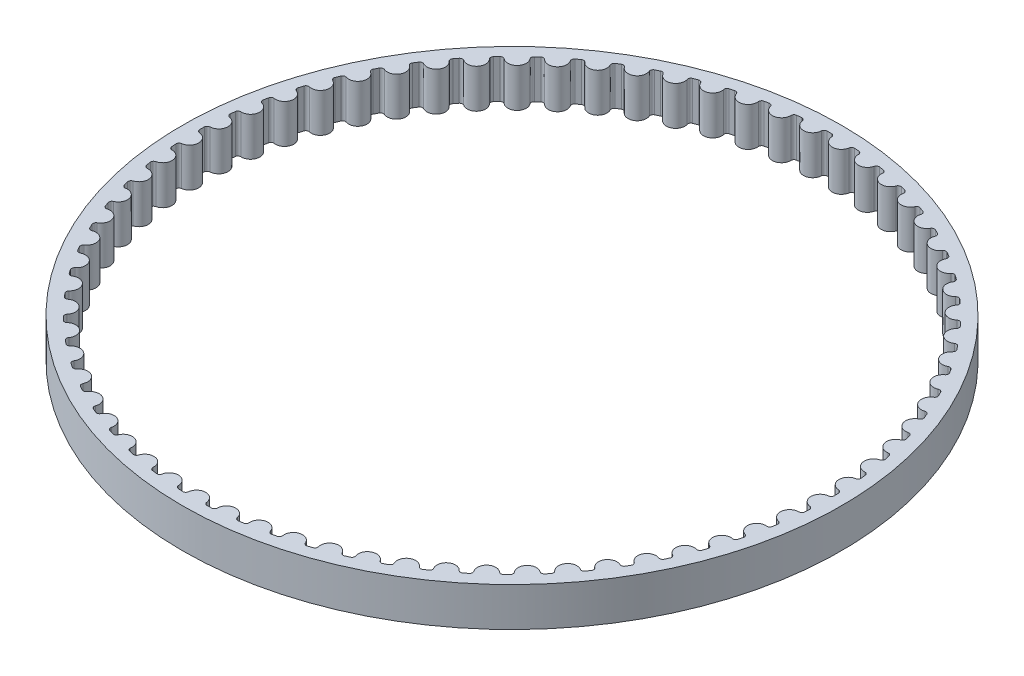
SolidWorks part; units mm, degrees
ref_plane "Front Plane" through (0, 0, 0) normal (0, 0, 1) x (1, 0, 0)
ref_plane "Top Plane" through (0, 0, 0) normal (0, 1, 0) x (1, 0, 0)
ref_plane "Right Plane" through (0, 0, 0) normal (1, 0, 0) x (0, 0, -1)
sketch "Sketch1" plane through (0, 0, 0) normal (0, 1, 0) x (1, 0, 0)
  circle A0 centre (0, 0) radius 33.8241
  arc B0 (-1.7169, -32.5188) -> (-1.2473, -32.5402) centre (0, 0) ccw
  arc B1 (-1.2473, -32.5402) -> (-0.9385, -32.2732) centre (-1.2358, -32.2414) ccw
  arc B2 (0.9385, -32.2732) -> (-0.9385, -32.2732) centre (0, -32.3736) ccw
  arc B3 (0.9385, -32.2732) -> (1.2473, -32.5402) centre (1.2358, -32.2414) ccw
  arc B4 (1.2473, -32.5402) -> (1.7169, -32.5188) centre (0, 0) ccw
  arc B5 (1.7169, -32.5188) -> (2.0001, -32.2248) centre (1.7011, -32.2202) ccw
  arc B6 (3.8694, -32.0541) -> (2.0001, -32.2248) centre (2.9439, -32.2394) ccw
  arc B7 (3.8694, -32.0541) -> (4.2012, -32.2919) centre (4.1626, -31.9954) ccw
  arc B8 (4.2012, -32.2919) -> (4.6669, -32.2279) centre (0, 0) ccw
  arc B9 (4.6669, -32.2279) -> (4.9222, -31.9094) centre (4.624, -31.932) ccw
  arc B10 (6.7682, -31.5695) -> (4.9222, -31.9094) centre (5.8634, -31.8382) ccw
  arc B11 (6.7682, -31.5695) -> (7.1202, -31.7761) centre (7.0548, -31.4843) ccw
  arc B12 (7.1202, -31.7761) -> (7.5782, -31.67) centre (0, 0) ccw
  arc B13 (7.5782, -31.67) -> (7.8035, -31.3296) centre (7.5086, -31.3792) ccw
  arc B14 (9.6109, -30.8232) -> (7.8035, -31.3296) centre (8.7343, -31.1731) ccw
  arc B15 (9.6109, -30.8232) -> (9.9803, -30.997) centre (9.8886, -30.7124) ccw
  arc B16 (9.9803, -30.997) -> (10.4267, -30.8497) centre (0, 0) ccw
  arc B17 (10.4267, -30.8497) -> (10.6201, -30.4902) centre (10.331, -30.5664) ccw
  arc B18 (12.374, -29.8215) -> (10.6201, -30.4902) centre (11.5328, -30.2497) ccw
  arc B19 (12.374, -29.8215) -> (12.7576, -29.961) centre (12.6405, -29.6859) ccw
  arc B20 (12.7576, -29.961) -> (13.1888, -29.7737) centre (0, 0) ccw
  arc B21 (13.1888, -29.7737) -> (13.3487, -29.3982) centre (13.0677, -29.5003) ccw
  arc B22 (15.0346, -28.5727) -> (13.3487, -29.3982) centre (14.2358, -29.0756) ccw
  arc B23 (15.0346, -28.5727) -> (15.4293, -28.6768) centre (15.2876, -28.4135) ccw
  arc B24 (15.4293, -28.6768) -> (15.8416, -28.451) centre (0, 0) ccw
  arc B25 (15.8416, -28.451) -> (15.9667, -28.0625) centre (15.6962, -28.1898) ccw
  arc B26 (17.5705, -27.0872) -> (15.9667, -28.0625) centre (16.8208, -27.6606) ccw
  arc B27 (17.5705, -27.0872) -> (17.9731, -27.1549) centre (17.808, -26.9056) ccw
  arc B28 (17.9731, -27.1549) -> (18.3632, -26.8926) centre (0, 0) ccw
  arc B29 (18.3632, -26.8926) -> (18.4524, -26.4943) centre (18.1946, -26.6457) ccw
  arc B30 (19.9609, -25.3772) -> (18.4524, -26.4943) centre (19.2664, -26.0164) ccw
  arc B31 (19.9609, -25.3772) -> (20.3679, -25.408) centre (20.1809, -25.1747) ccw
  arc B32 (20.3679, -25.408) -> (20.7326, -25.1113) centre (0, 0) ccw
  arc B33 (20.7326, -25.1113) -> (20.7852, -24.7066) centre (20.5422, -24.8808) ccw
  arc B34 (22.1859, -23.4569) -> (20.7852, -24.7066) centre (21.5524, -24.1566) ccw
  arc B35 (22.1859, -23.4569) -> (22.594, -23.4506) centre (22.3866, -23.2353) ccw
  arc B36 (22.594, -23.4506) -> (22.9302, -23.122) centre (0, 0) ccw
  arc B37 (22.9302, -23.122) -> (22.9458, -22.7141) centre (22.7196, -22.9097) ccw
  arc B38 (24.227, -21.3423) -> (22.9458, -22.7141) centre (23.6598, -22.0967) ccw
  arc B39 (24.227, -21.3423) -> (24.6329, -21.2988) centre (24.4067, -21.1033) ccw
  arc B40 (24.6329, -21.2988) -> (24.9378, -20.941) centre (0, 0) ccw
  arc B41 (24.9378, -20.941) -> (24.9162, -20.5334) centre (24.7088, -20.7487) ccw
  arc B42 (26.0674, -19.0508) -> (24.9162, -20.5334) centre (25.5711, -19.8536) ccw
  arc B43 (26.0674, -19.0508) -> (26.4676, -18.9706) centre (26.2246, -18.7964) ccw
  arc B44 (26.4676, -18.9706) -> (26.7387, -18.5865) centre (0, 0) ccw
  arc B45 (26.7387, -18.5865) -> (26.6802, -18.1826) centre (26.4932, -18.4159) ccw
  arc B46 (27.6918, -16.6014) -> (26.6802, -18.1826) centre (27.2705, -17.4461) ccw
  arc B47 (27.6918, -16.6014) -> (28.0831, -16.4852) centre (27.8252, -16.3338) ccw
  arc B48 (28.0831, -16.4852) -> (28.3181, -16.078) centre (0, 0) ccw
  arc B49 (28.3181, -16.078) -> (28.2231, -15.6811) centre (28.0581, -15.9304) ccw
  arc B50 (29.0867, -14.0145) -> (28.2231, -15.6811) centre (28.744, -14.8939) ccw
  arc B51 (29.0867, -14.0145) -> (29.4658, -13.8631) centre (29.1952, -13.7359) ccw
  arc B52 (29.4658, -13.8631) -> (29.6628, -13.4363) centre (0, 0) ccw
  arc B53 (29.6628, -13.4363) -> (29.5321, -13.0496) centre (29.3905, -13.313) ccw
  arc B54 (30.2406, -11.3114) -> (29.5321, -13.0496) centre (29.9793, -12.2184) ccw
  arc B55 (30.2406, -11.3114) -> (30.6043, -11.1262) centre (30.3233, -11.0241) ccw
  arc B56 (30.6043, -11.1262) -> (30.7618, -10.6833) centre (0, 0) ccw
  arc B57 (30.7618, -10.6833) -> (30.5964, -10.3101) centre (30.4793, -10.5852) ccw
  arc B58 (31.1439, -8.5146) -> (30.5964, -10.3101) centre (30.9662, -9.4416) ccw
  arc B59 (31.1439, -8.5146) -> (31.4893, -8.2971) centre (31.2002, -8.221) ccw
  arc B60 (31.4893, -8.2971) -> (31.6058, -7.8417) centre (0, 0) ccw
  arc B61 (31.6058, -7.8417) -> (31.4072, -7.4851) centre (31.3156, -7.7697) ccw
  arc B62 (31.7891, -5.6473) -> (31.4072, -7.4851) centre (31.6965, -6.5866) ccw
  arc B63 (31.7891, -5.6473) -> (32.1133, -5.3993) centre (31.8185, -5.3497) ccw
  arc B64 (32.1133, -5.3993) -> (32.1879, -4.9351) centre (0, 0) ccw
  arc B65 (32.1879, -4.9351) -> (31.9578, -4.5981) centre (31.8924, -4.8898) ccw
  arc B66 (32.1709, -2.7331) -> (31.9578, -4.5981) centre (32.1641, -3.677) ccw
  arc B67 (32.1709, -2.7331) -> (32.4713, -2.4567) centre (32.1731, -2.4341) ccw
  arc B68 (32.4713, -2.4567) -> (32.5034, -1.9877) centre (0, 0) ccw
  arc B69 (32.5034, -1.9877) -> (32.2435, -1.6729) centre (32.2049, -1.9694) ccw
  arc B70 (32.2862, 0.2036) -> (32.2435, -1.6729) centre (32.3652, -0.7369) ccw
  arc B71 (32.2862, 0.2036) -> (32.5601, 0.5062) centre (32.2612, 0.5016) ccw
  arc B72 (32.5601, 0.5062) -> (32.5494, 0.9762) centre (0, 0) ccw
  arc B73 (32.5494, 0.9762) -> (32.262, 1.2661) centre (32.2506, 0.9673) ccw
  arc B74 (32.1339, 3.1387) -> (32.262, 1.2661) centre (32.2981, 2.2093) ccw
  arc B75 (32.1339, 3.1387) -> (32.3792, 3.465) centre (32.0819, 3.4332) ccw
  arc B76 (32.3792, 3.465) -> (32.3258, 3.9321) centre (0, 0) ccw
  arc B77 (32.3258, 3.9321) -> (32.0132, 4.1946) centre (32.029, 3.896) ccw
  arc B78 (31.7154, 6.0478) -> (32.0132, 4.1946) centre (31.9634, 5.1371) ccw
  arc B79 (31.7154, 6.0478) -> (31.93, 6.395) centre (31.6368, 6.3363) ccw
  arc B80 (31.93, 6.395) -> (31.8343, 6.8553) centre (0, 0) ccw
  arc B81 (31.8343, 6.8553) -> (31.4991, 7.0883) centre (31.542, 6.7924) ccw
  arc B82 (31.034, 8.9068) -> (31.4991, 7.0883) centre (31.3638, 8.0224) ccw
  arc B83 (31.034, 8.9068) -> (31.2161, 9.2721) centre (30.9295, 9.187) ccw
  arc B84 (31.2161, 9.2721) -> (31.079, 9.7218) centre (0, 0) ccw
  arc B85 (31.079, 9.7218) -> (30.7241, 9.9233) centre (30.7937, 9.6325) ccw
  arc B86 (30.0955, 11.692) -> (30.7241, 9.9233) centre (30.5044, 10.8412) ccw
  arc B87 (30.0955, 11.692) -> (30.2436, 12.0723) centre (29.966, 11.9615) ccw
  arc B88 (30.2436, 12.0723) -> (30.0662, 12.5077) centre (0, 0) ccw
  arc B89 (30.0662, 12.5077) -> (29.6944, 12.6761) centre (29.7902, 12.3928) ccw
  arc B90 (28.9076, 14.3803) -> (29.6944, 12.6761) centre (29.3921, 13.5702) ccw
  arc B91 (28.9076, 14.3803) -> (29.0205, 14.7725) centre (28.7541, 14.6369) ccw
  arc B92 (29.0205, 14.7725) -> (28.8043, 15.1899) centre (0, 0) ccw
  arc B93 (28.8043, 15.1899) -> (28.4187, 15.3238) centre (28.5398, 15.0504) ccw
  arc B94 (27.4801, 16.9494) -> (28.4187, 15.3238) centre (28.0363, 16.1868) ccw
  arc B95 (27.4801, 16.9494) -> (27.557, 17.3503) centre (27.3039, 17.191) ccw
  arc B96 (27.557, 17.3503) -> (27.3036, 17.7463) centre (0, 0) ccw
  arc B97 (27.3036, 17.7463) -> (26.9075, 17.8446) centre (27.0529, 17.5833) ccw
  arc B98 (25.825, 19.3781) -> (26.9075, 17.8446) centre (26.4482, 18.6692) ccw
  arc B99 (25.825, 19.3781) -> (25.8651, 19.7843) centre (25.6276, 19.6026) ccw
  arc B100 (25.8651, 19.7843) -> (25.5768, 20.1556) centre (0, 0) ccw
  arc B101 (25.5768, 20.1556) -> (25.1733, 20.2175) centre (25.3419, 19.9705) ccw
  arc B102 (23.9559, 21.6462) -> (25.1733, 20.2175) centre (24.641, 20.9969) ccw
  arc B103 (23.9559, 21.6462) -> (23.9588, 22.0543) centre (23.7388, 21.8518) ccw
  arc B104 (23.9588, 22.0543) -> (23.6379, 22.3979) centre (0, 0) ccw
  arc B105 (23.6379, 22.3979) -> (23.2305, 22.4228) centre (23.4209, 22.1923) ccw
  arc B106 (21.8882, 23.7349) -> (23.2305, 22.4228) centre (22.6295, 23.1506) ccw
  arc B107 (21.8882, 23.7349) -> (21.854, 24.1417) centre (21.6534, 23.92) ccw
  arc B108 (21.854, 24.1417) -> (21.5033, 24.4546) centre (0, 0) ccw
  arc B109 (21.5033, 24.4546) -> (21.0953, 24.4424) centre (21.3058, 24.2301) ccw
  arc B110 (19.6392, 25.627) -> (21.0953, 24.4424) centre (20.4306, 25.1125) ccw
  arc B111 (19.6392, 25.627) -> (19.5682, 26.0289) centre (19.3885, 25.7899) ccw
  arc B112 (19.5682, 26.0289) -> (19.1904, 26.3087) centre (0, 0) ccw
  arc B113 (19.1904, 26.3087) -> (18.7852, 26.2594) centre (19.0142, 26.0671) ccw
  arc B114 (17.2274, 27.3067) -> (18.7852, 26.2594) centre (18.0623, 26.8664) ccw
  arc B115 (17.2274, 27.3067) -> (17.1202, 27.7005) centre (16.963, 27.4462) ccw
  arc B116 (17.1202, 27.7005) -> (16.7185, 27.9448) centre (0, 0) ccw
  arc B117 (16.7185, 27.9448) -> (16.3195, 27.8588) centre (16.565, 27.6882) ccw
  arc B118 (14.6729, 28.7601) -> (16.3195, 27.8588) centre (15.5444, 28.3975) ccw
  arc B119 (14.6729, 28.7601) -> (14.5303, 29.1426) centre (14.3969, 28.875) ccw
  arc B120 (14.5303, 29.1426) -> (14.1081, 29.3493) centre (0, 0) ccw
  arc B121 (14.1081, 29.3493) -> (13.7185, 29.2274) centre (13.9785, 29.0798) ccw
  arc B122 (11.9968, 29.9753) -> (13.7185, 29.2274) centre (12.8977, 29.6934) ccw
  arc B123 (11.9968, 29.9753) -> (11.82, 30.3431) centre (11.7115, 30.0645) ccw
  arc B124 (11.82, 30.3431) -> (11.3807, 30.5106) centre (0, 0) ccw
  arc B125 (11.3807, 30.5106) -> (11.0039, 30.3538) centre (11.2762, 30.2305) ccw
  arc B126 (9.2213, 30.942) -> (11.0039, 30.3538) centre (10.1441, 30.7432) ccw
  arc B127 (9.2213, 30.942) -> (9.0118, 31.2923) centre (8.929, 31.005) ccw
  arc B128 (9.0118, 31.2923) -> (8.5591, 31.4191) centre (0, 0) ccw
  arc B129 (8.5591, 31.4191) -> (8.1981, 31.2287) centre (8.4805, 31.1306) ccw
  arc B130 (6.3694, 31.6523) -> (8.1981, 31.2287) centre (7.3064, 31.5383) ccw
  arc B131 (6.3694, 31.6523) -> (6.1289, 31.9821) centre (6.0726, 31.6885) ccw
  arc B132 (6.1289, 31.9821) -> (5.6666, 32.0673) centre (0, 0) ccw
  arc B133 (5.6666, 32.0673) -> (5.3243, 31.8448) centre (5.6145, 31.7728) ccw
  arc B134 (3.4647, 32.1004) -> (5.3243, 31.8448) centre (4.4082, 32.072) ccw
  arc B135 (3.4647, 32.1004) -> (3.1952, 32.4069) centre (3.1659, 32.1094) ccw
  arc B136 (3.1952, 32.4069) -> (2.7271, 32.4497) centre (0, 0) ccw
  arc B137 (2.7271, 32.4497) -> (2.4065, 32.197) centre (2.702, 32.1517) ccw
  arc B138 (0.5313, 32.2825) -> (2.4065, 32.197) centre (1.4735, 32.34) ccw
  arc B139 (0.5313, 32.2825) -> (0.2351, 32.5632) centre (0.2329, 32.2642) ccw
  arc B140 (0.2351, 32.5632) -> (-0.2351, 32.5632) centre (0, 0) ccw
  arc B141 (-0.2351, 32.5632) -> (-0.5313, 32.2825) centre (-0.2329, 32.2642) ccw
  arc B142 (-2.4065, 32.197) -> (-0.5313, 32.2825) centre (-1.4735, 32.34) ccw
  arc B143 (-2.4065, 32.197) -> (-2.7271, 32.4497) centre (-2.702, 32.1517) ccw
  arc B144 (-2.7271, 32.4497) -> (-3.1952, 32.4069) centre (0, 0) ccw
  arc B145 (-3.1952, 32.4069) -> (-3.4647, 32.1004) centre (-3.1659, 32.1094) ccw
  arc B146 (-5.3243, 31.8448) -> (-3.4647, 32.1004) centre (-4.4082, 32.072) ccw
  arc B147 (-5.3243, 31.8448) -> (-5.6666, 32.0673) centre (-5.6145, 31.7728) ccw
  arc B148 (-5.6666, 32.0673) -> (-6.1289, 31.9821) centre (0, 0) ccw
  arc B149 (-6.1289, 31.9821) -> (-6.3694, 31.6523) centre (-6.0726, 31.6885) ccw
  arc B150 (-8.1981, 31.2287) -> (-6.3694, 31.6523) centre (-7.3064, 31.5383) ccw
  arc B151 (-8.1981, 31.2287) -> (-8.5591, 31.4191) centre (-8.4805, 31.1306) ccw
  arc B152 (-8.5591, 31.4191) -> (-9.0118, 31.2923) centre (0, 0) ccw
  arc B153 (-9.0118, 31.2923) -> (-9.2213, 30.942) centre (-8.929, 31.005) ccw
  arc B154 (-11.0039, 30.3538) -> (-9.2213, 30.942) centre (-10.1441, 30.7432) ccw
  arc B155 (-11.0039, 30.3538) -> (-11.3807, 30.5106) centre (-11.2762, 30.2305) ccw
  arc B156 (-11.3807, 30.5106) -> (-11.82, 30.3431) centre (0, 0) ccw
  arc B157 (-11.82, 30.3431) -> (-11.9968, 29.9753) centre (-11.7115, 30.0645) ccw
  arc B158 (-13.7185, 29.2274) -> (-11.9968, 29.9753) centre (-12.8977, 29.6934) ccw
  arc B159 (-13.7185, 29.2274) -> (-14.1081, 29.3493) centre (-13.9785, 29.0798) ccw
  arc B160 (-14.1081, 29.3493) -> (-14.5303, 29.1426) centre (0, 0) ccw
  arc B161 (-14.5303, 29.1426) -> (-14.6729, 28.7601) centre (-14.3969, 28.875) ccw
  arc B162 (-16.3195, 27.8588) -> (-14.6729, 28.7601) centre (-15.5444, 28.3975) ccw
  arc B163 (-16.3195, 27.8588) -> (-16.7185, 27.9448) centre (-16.565, 27.6882) ccw
  arc B164 (-16.7185, 27.9448) -> (-17.1202, 27.7005) centre (0, 0) ccw
  arc B165 (-17.1202, 27.7005) -> (-17.2274, 27.3067) centre (-16.963, 27.4462) ccw
  arc B166 (-18.7852, 26.2594) -> (-17.2274, 27.3067) centre (-18.0623, 26.8664) ccw
  arc B167 (-18.7852, 26.2594) -> (-19.1904, 26.3087) centre (-19.0142, 26.0671) ccw
  arc B168 (-19.1904, 26.3087) -> (-19.5682, 26.0289) centre (0, 0) ccw
  arc B169 (-19.5682, 26.0289) -> (-19.6392, 25.627) centre (-19.3885, 25.7899) ccw
  arc B170 (-21.0953, 24.4424) -> (-19.6392, 25.627) centre (-20.4306, 25.1125) ccw
  arc B171 (-21.0953, 24.4424) -> (-21.5033, 24.4546) centre (-21.3058, 24.2301) ccw
  arc B172 (-21.5033, 24.4546) -> (-21.854, 24.1417) centre (0, 0) ccw
  arc B173 (-21.854, 24.1417) -> (-21.8882, 23.7349) centre (-21.6534, 23.92) ccw
  arc B174 (-23.2305, 22.4228) -> (-21.8882, 23.7349) centre (-22.6295, 23.1506) ccw
  arc B175 (-23.2305, 22.4228) -> (-23.6379, 22.3979) centre (-23.4209, 22.1923) ccw
  arc B176 (-23.6379, 22.3979) -> (-23.9588, 22.0543) centre (0, 0) ccw
  arc B177 (-23.9588, 22.0543) -> (-23.9559, 21.6462) centre (-23.7388, 21.8518) ccw
  arc B178 (-25.1733, 20.2175) -> (-23.9559, 21.6462) centre (-24.641, 20.9969) ccw
  arc B179 (-25.1733, 20.2175) -> (-25.5768, 20.1556) centre (-25.3419, 19.9705) ccw
  arc B180 (-25.5768, 20.1556) -> (-25.8651, 19.7843) centre (0, 0) ccw
  arc B181 (-25.8651, 19.7843) -> (-25.825, 19.3781) centre (-25.6276, 19.6026) ccw
  arc B182 (-26.9075, 17.8446) -> (-25.825, 19.3781) centre (-26.4482, 18.6692) ccw
  arc B183 (-26.9075, 17.8446) -> (-27.3036, 17.7463) centre (-27.0529, 17.5833) ccw
  arc B184 (-27.3036, 17.7463) -> (-27.557, 17.3503) centre (0, 0) ccw
  arc B185 (-27.557, 17.3503) -> (-27.4801, 16.9494) centre (-27.3039, 17.191) ccw
  arc B186 (-28.4187, 15.3238) -> (-27.4801, 16.9494) centre (-28.0363, 16.1868) ccw
  arc B187 (-28.4187, 15.3238) -> (-28.8043, 15.1899) centre (-28.5398, 15.0504) ccw
  arc B188 (-28.8043, 15.1899) -> (-29.0205, 14.7725) centre (0, 0) ccw
  arc B189 (-29.0205, 14.7725) -> (-28.9076, 14.3803) centre (-28.7541, 14.6369) ccw
  arc B190 (-29.6944, 12.6761) -> (-28.9076, 14.3803) centre (-29.3921, 13.5702) ccw
  arc B191 (-29.6944, 12.6761) -> (-30.0662, 12.5077) centre (-29.7902, 12.3928) ccw
  arc B192 (-30.0662, 12.5077) -> (-30.2436, 12.0723) centre (0, 0) ccw
  arc B193 (-30.2436, 12.0723) -> (-30.0955, 11.692) centre (-29.966, 11.9615) ccw
  arc B194 (-30.7241, 9.9233) -> (-30.0955, 11.692) centre (-30.5044, 10.8412) ccw
  arc B195 (-30.7241, 9.9233) -> (-31.079, 9.7218) centre (-30.7937, 9.6325) ccw
  arc B196 (-31.079, 9.7218) -> (-31.2161, 9.2721) centre (0, 0) ccw
  arc B197 (-31.2161, 9.2721) -> (-31.034, 8.9068) centre (-30.9295, 9.187) ccw
  arc B198 (-31.4991, 7.0883) -> (-31.034, 8.9068) centre (-31.3638, 8.0224) ccw
  arc B199 (-31.4991, 7.0883) -> (-31.8343, 6.8553) centre (-31.542, 6.7924) ccw
  arc B200 (-31.8343, 6.8553) -> (-31.93, 6.395) centre (0, 0) ccw
  arc B201 (-31.93, 6.395) -> (-31.7154, 6.0478) centre (-31.6368, 6.3363) ccw
  arc B202 (-32.0132, 4.1946) -> (-31.7154, 6.0478) centre (-31.9634, 5.1371) ccw
  arc B203 (-32.0132, 4.1946) -> (-32.3258, 3.9321) centre (-32.029, 3.896) ccw
  arc B204 (-32.3258, 3.9321) -> (-32.3792, 3.465) centre (0, 0) ccw
  arc B205 (-32.3792, 3.465) -> (-32.1339, 3.1387) centre (-32.0819, 3.4332) ccw
  arc B206 (-32.262, 1.2661) -> (-32.1339, 3.1387) centre (-32.2981, 2.2093) ccw
  arc B207 (-32.262, 1.2661) -> (-32.5494, 0.9762) centre (-32.2506, 0.9673) ccw
  arc B208 (-32.5494, 0.9762) -> (-32.5601, 0.5062) centre (0, 0) ccw
  arc B209 (-32.5601, 0.5062) -> (-32.2862, 0.2036) centre (-32.2612, 0.5016) ccw
  arc B210 (-32.2435, -1.6729) -> (-32.2862, 0.2036) centre (-32.3652, -0.7369) ccw
  arc B211 (-32.2435, -1.6729) -> (-32.5034, -1.9877) centre (-32.2049, -1.9694) ccw
  arc B212 (-32.5034, -1.9877) -> (-32.4713, -2.4567) centre (0, 0) ccw
  arc B213 (-32.4713, -2.4567) -> (-32.1709, -2.7331) centre (-32.1731, -2.4341) ccw
  arc B214 (-31.9578, -4.5981) -> (-32.1709, -2.7331) centre (-32.1641, -3.677) ccw
  arc B215 (-31.9578, -4.5981) -> (-32.1879, -4.9351) centre (-31.8924, -4.8898) ccw
  arc B216 (-32.1879, -4.9351) -> (-32.1133, -5.3993) centre (0, 0) ccw
  arc B217 (-32.1133, -5.3993) -> (-31.7891, -5.6473) centre (-31.8185, -5.3497) ccw
  arc B218 (-31.4072, -7.4851) -> (-31.7891, -5.6473) centre (-31.6965, -6.5866) ccw
  arc B219 (-31.4072, -7.4851) -> (-31.6058, -7.8417) centre (-31.3156, -7.7697) ccw
  arc B220 (-31.6058, -7.8417) -> (-31.4893, -8.2971) centre (0, 0) ccw
  arc B221 (-31.4893, -8.2971) -> (-31.1439, -8.5146) centre (-31.2002, -8.221) ccw
  arc B222 (-30.5964, -10.3101) -> (-31.1439, -8.5146) centre (-30.9662, -9.4416) ccw
  arc B223 (-30.5964, -10.3101) -> (-30.7618, -10.6833) centre (-30.4793, -10.5852) ccw
  arc B224 (-30.7618, -10.6833) -> (-30.6043, -11.1262) centre (0, 0) ccw
  arc B225 (-30.6043, -11.1262) -> (-30.2406, -11.3114) centre (-30.3233, -11.0241) ccw
  arc B226 (-29.5321, -13.0496) -> (-30.2406, -11.3114) centre (-29.9793, -12.2184) ccw
  arc B227 (-29.5321, -13.0496) -> (-29.6628, -13.4363) centre (-29.3905, -13.313) ccw
  arc B228 (-29.6628, -13.4363) -> (-29.4658, -13.8631) centre (0, 0) ccw
  arc B229 (-29.4658, -13.8631) -> (-29.0867, -14.0145) centre (-29.1952, -13.7359) ccw
  arc B230 (-28.2231, -15.6811) -> (-29.0867, -14.0145) centre (-28.744, -14.8939) ccw
  arc B231 (-28.2231, -15.6811) -> (-28.3181, -16.078) centre (-28.0581, -15.9304) ccw
  arc B232 (-28.3181, -16.078) -> (-28.0831, -16.4852) centre (0, 0) ccw
  arc B233 (-28.0831, -16.4852) -> (-27.6918, -16.6014) centre (-27.8252, -16.3338) ccw
  arc B234 (-26.6802, -18.1826) -> (-27.6918, -16.6014) centre (-27.2705, -17.4461) ccw
  arc B235 (-26.6802, -18.1826) -> (-26.7387, -18.5865) centre (-26.4932, -18.4159) ccw
  arc B236 (-26.7387, -18.5865) -> (-26.4676, -18.9706) centre (0, 0) ccw
  arc B237 (-26.4676, -18.9706) -> (-26.0674, -19.0508) centre (-26.2246, -18.7964) ccw
  arc B238 (-24.9162, -20.5334) -> (-26.0674, -19.0508) centre (-25.5711, -19.8536) ccw
  arc B239 (-24.9162, -20.5334) -> (-24.9378, -20.941) centre (-24.7088, -20.7487) ccw
  arc B240 (-24.9378, -20.941) -> (-24.6329, -21.2988) centre (0, 0) ccw
  arc B241 (-24.6329, -21.2988) -> (-24.227, -21.3423) centre (-24.4067, -21.1033) ccw
  arc B242 (-22.9458, -22.7141) -> (-24.227, -21.3423) centre (-23.6598, -22.0967) ccw
  arc B243 (-22.9458, -22.7141) -> (-22.9302, -23.122) centre (-22.7196, -22.9097) ccw
  arc B244 (-22.9302, -23.122) -> (-22.594, -23.4506) centre (0, 0) ccw
  arc B245 (-22.594, -23.4506) -> (-22.1859, -23.4569) centre (-22.3866, -23.2353) ccw
  arc B246 (-20.7852, -24.7066) -> (-22.1859, -23.4569) centre (-21.5524, -24.1566) ccw
  arc B247 (-20.7852, -24.7066) -> (-20.7326, -25.1113) centre (-20.5422, -24.8808) ccw
  arc B248 (-20.7326, -25.1113) -> (-20.3679, -25.408) centre (0, 0) ccw
  arc B249 (-20.3679, -25.408) -> (-19.9609, -25.3772) centre (-20.1809, -25.1747) ccw
  arc B250 (-18.4524, -26.4943) -> (-19.9609, -25.3772) centre (-19.2664, -26.0164) ccw
  arc B251 (-18.4524, -26.4943) -> (-18.3632, -26.8926) centre (-18.1946, -26.6457) ccw
  arc B252 (-18.3632, -26.8926) -> (-17.9731, -27.1549) centre (0, 0) ccw
  arc B253 (-17.9731, -27.1549) -> (-17.5705, -27.0872) centre (-17.808, -26.9056) ccw
  arc B254 (-15.9667, -28.0625) -> (-17.5705, -27.0872) centre (-16.8208, -27.6606) ccw
  arc B255 (-15.9667, -28.0625) -> (-15.8416, -28.451) centre (-15.6962, -28.1898) ccw
  arc B256 (-15.8416, -28.451) -> (-15.4293, -28.6768) centre (0, 0) ccw
  arc B257 (-15.4293, -28.6768) -> (-15.0346, -28.5727) centre (-15.2876, -28.4135) ccw
  arc B258 (-13.3487, -29.3982) -> (-15.0346, -28.5727) centre (-14.2358, -29.0756) ccw
  arc B259 (-13.3487, -29.3982) -> (-13.1888, -29.7737) centre (-13.0677, -29.5003) ccw
  arc B260 (-13.1888, -29.7737) -> (-12.7576, -29.961) centre (0, 0) ccw
  arc B261 (-12.7576, -29.961) -> (-12.374, -29.8215) centre (-12.6405, -29.6859) ccw
  arc B262 (-10.6201, -30.4902) -> (-12.374, -29.8215) centre (-11.5328, -30.2497) ccw
  arc B263 (-10.6201, -30.4902) -> (-10.4267, -30.8497) centre (-10.331, -30.5664) ccw
  arc B264 (-10.4267, -30.8497) -> (-9.9803, -30.997) centre (0, 0) ccw
  arc B265 (-9.9803, -30.997) -> (-9.6109, -30.8232) centre (-9.8886, -30.7124) ccw
  arc B266 (-7.8035, -31.3296) -> (-9.6109, -30.8232) centre (-8.7343, -31.1731) ccw
  arc B267 (-7.8035, -31.3296) -> (-7.5782, -31.67) centre (-7.5086, -31.3792) ccw
  arc B268 (-7.5782, -31.67) -> (-7.1202, -31.7761) centre (0, 0) ccw
  arc B269 (-7.1202, -31.7761) -> (-6.7682, -31.5695) centre (-7.0548, -31.4843) ccw
  arc B270 (-4.9222, -31.9094) -> (-6.7682, -31.5695) centre (-5.8634, -31.8382) ccw
  arc B271 (-4.9222, -31.9094) -> (-4.6669, -32.2279) centre (-4.624, -31.932) ccw
  arc B272 (-4.6669, -32.2279) -> (-4.2012, -32.2919) centre (0, 0) ccw
  arc B273 (-4.2012, -32.2919) -> (-3.8694, -32.0541) centre (-4.1626, -31.9954) ccw
  arc B274 (-2.0001, -32.2248) -> (-3.8694, -32.0541) centre (-2.9439, -32.2394) ccw
  arc B275 (-2.0001, -32.2248) -> (-1.7169, -32.5188) centre (-1.7011, -32.2202) ccw
  dimension "D1" = 1.26
sketch_block_instance "Block-69T GT2 Pulley-1"
sketch_block "Block-69T GT2 Pulley"
extrude "Boss-Extrude1" add sketch "Sketch1" along normal blind 4
